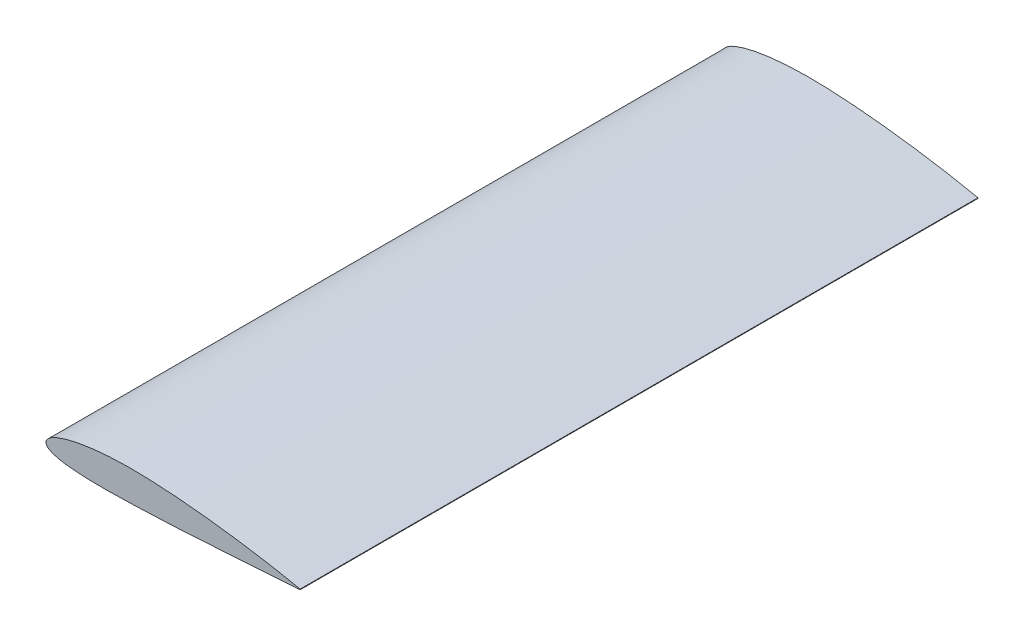
SolidWorks part; units mm, degrees
ref_plane "Plano frontal" through (0, 0, 0) normal (0, 0, 1) x (1, 0, 0)
ref_plane "Plano superior" through (0, 0, 0) normal (0, 1, 0) x (1, 0, 0)
ref_plane "Plano direito" through (0, 0, 0) normal (1, 0, 0) x (0, 0, -1)
curve "Curva1"
  spline degree 3 poles (1500.126, 1.8855, 0) (1499.3625, 2.0445, 0) (1496.3129, 2.6798, 0) (1489.4682, 4.1005, 0) (1478.1042, 6.4388, 0) (1462.2859, 9.6487, 0) (1442.1065, 13.6771, 0) (1417.6826, 18.4488, 0) (1389.1576, 23.8816, 0) (1356.6995, 29.8872, 0) (1320.4993, 36.3634, 0) (1280.7733, 43.2092, 0) (1237.7583, 50.3211, 0) (1191.7122, 57.5897, 0) (1142.9127, 64.908, 0) (1091.6565, 72.1708, 0) (1038.2553, 79.2693, 0) (983.0355, 86.0986, 0) (926.3364, 92.5608, 0) (868.5069, 98.5429, 0) (809.906, 103.958, 0) (750.8975, 108.6967, 0) (691.8509, 112.6816, 0) (633.0689, 115.8185, 0) (574.8336, 118.0666, 0) (517.5037, 119.0124, 0) (461.5248, 118.6485, 0) (407.3522, 116.9664, 0) (355.3439, 113.9866, 0) (305.8441, 109.7533, 0) (259.1775, 104.3411, 0) (215.649, 97.8407, 0) (175.5378, 90.3672, 0) (139.0976, 82.0473, 0) (106.5485, 73.0302, 0) (78.0829, 63.455, 0) (53.8515, 53.474, 0) (33.9673, 43.2199, 0) (18.4797, 32.7946, 0) (7.3977, 22.2197, 0) (0.7283, 11.2851, 0) (-0.8552, -0.0857, 0) (2.9436, -10.908, 0) (11.5766, -20.3167, 0) (24.3855, -28.5551, 0) (41.3662, -35.8908, 0) (62.4903, -42.3613, 0) (87.6694, -47.9739, 0) (116.7658, -52.7143, 0) (149.6083, -56.5782, 0) (185.9998, -59.5718, 0) (225.7233, -61.7205, 0) (268.5449, -63.0584, 0) (314.2151, -63.6414, 0) (362.4709, -63.5326, 0) (413.036, -62.8185, 0) (465.6225, -61.5859, 0) (519.931, -59.9419, 0) (575.7379, -57.9731, 0) (632.7892, -55.8169, 0) (690.7338, -53.2094, 0) (749.1366, -50.2811, 0) (807.5763, -47.0959, 0) (865.6983, -43.7442, 0) (923.1476, -40.287, 0) (979.572, -36.7918, 0) (1034.6232, -33.3034, 0) (1087.9613, -29.8708, 0) (1139.2546, -26.5308, 0) (1188.1829, -23.3117, 0) (1234.439, -20.2431, 0) (1277.7318, -17.3413, 0) (1317.7874, -14.6353, 0) (1354.3513, -12.1386, 0) (1387.1898, -9.875, 0) (1416.0927, -7.8608, 0) (1440.874, -6.1152, 0) (1461.3734, -4.6599, 0) (1477.4577, -3.5066, 0) (1489.0222, -2.6742, 0) (1495.991, -2.1677, 0) (1499.0965, -1.942, 0) (1499.874, -1.8855, 0) knots 0 0 0 0 0.000764 0.003052 0.00685 0.012132 0.018868 0.027013 0.036517 0.047321 0.059357 0.072551 0.08682 0.102077 0.118228 0.135171 0.152802 0.171013 0.18969 0.208718 0.227979 0.247354 0.266723 0.285966 0.305032 0.323824 0.342144 0.35988 0.376926 0.393182 0.408553 0.422951 0.436298 0.448523 0.459565 0.469379 0.477934 0.48522 0.491268 0.496168 0.500133 0.503587 0.507041 0.511 0.515876 0.521872 0.529071 0.537495 0.547131 0.557945 0.56989 0.582904 0.596922 0.611866 0.627656 0.644204 0.661417 0.679197 0.697443 0.716134 0.735139 0.754278 0.773432 0.792487 0.811323 0.829826 0.84788 0.865374 0.882198 0.898247 0.913421 0.927622 0.940763 0.952759 0.963533 0.973016 0.981148 0.987875 0.993154 0.996949 0.999236 1 1 1 1
sketch "Esboço2" plane through (0, 0, 0) normal (0, 0, 1) x (1, 0, 0)
  line L0 (1499.874, -1.8855) -> (1500.126, 1.8855)
  spline S0 degree 3 poles (2715.1019, 2700.4515) (1914.4321, -95.2232) (1704.9573, -40.6259) (1489.4682, 4.1005) (1478.1042, 6.4388) (1462.2859, 9.6487) (1442.1065, 13.6771) (1417.6826, 18.4488) (1389.1576, 23.8816) (1356.6995, 29.8872) (1320.4993, 36.3634) (1280.7733, 43.2092) (1237.7583, 50.3211) (1191.7122, 57.5897) (1142.9127, 64.908) (1091.6565, 72.1708) (1038.2553, 79.2693) (983.0355, 86.0986) (926.3364, 92.5608) (868.5069, 98.5429) (809.906, 103.958) (750.8975, 108.6967) (691.8509, 112.6816) (633.0689, 115.8185) (574.8336, 118.0666) (517.5037, 119.0124) (461.5248, 118.6485) (407.3522, 116.9664) (355.3439, 113.9866) (305.8441, 109.7533) (259.1775, 104.3411) (215.649, 97.8407) (175.5378, 90.3672) (139.0976, 82.0473) (106.5485, 73.0302) (78.0829, 63.455) (53.8515, 53.474) (33.9673, 43.2199) (18.4797, 32.7946) (7.3977, 22.2197) (0.7283, 11.2851) (-0.8552, -0.0857) (2.9436, -10.908) (11.5766, -20.3167) (24.3855, -28.5551) (41.3662, -35.8908) (62.4903, -42.3613) (87.6694, -47.9739) (116.7658, -52.7143) (149.6083, -56.5782) (185.9998, -59.5718) (225.7233, -61.7205) (268.5449, -63.0584) (314.2151, -63.6414) (362.4709, -63.5326) (413.036, -62.8185) (465.6225, -61.5859) (519.931, -59.9419) (575.7379, -57.9731) (632.7892, -55.8169) (690.7338, -53.2094) (749.1366, -50.2811) (807.5763, -47.0959) (865.6983, -43.7442) (923.1476, -40.287) (979.572, -36.7918) (1034.6232, -33.3034) (1087.9613, -29.8708) (1139.2546, -26.5308) (1188.1829, -23.3117) (1234.439, -20.2431) (1277.7318, -17.3413) (1317.7874, -14.6353) (1354.3513, -12.1386) (1387.1898, -9.875) (1416.0927, -7.8608) (1440.874, -6.1152) (1461.3734, -4.6599) (1477.4577, -3.5066) (1489.0222, -2.6742) (2096.1651, 41.4592) (2699.6397, 82.5696) (3151.3263, 2224.0389) knots -0.208799 -0.208799 -0.208799 -0.208799 0.000764 0.003052 0.00685 0.012132 0.018868 0.027013 0.036517 0.047321 0.059357 0.072551 0.08682 0.102077 0.118228 0.135171 0.152802 0.171013 0.18969 0.208718 0.227979 0.247354 0.266723 0.285966 0.305032 0.323824 0.342144 0.35988 0.376926 0.393182 0.408553 0.422951 0.436298 0.448523 0.459565 0.469379 0.477934 0.48522 0.491268 0.496168 0.500133 0.503587 0.507041 0.511 0.515876 0.521872 0.529071 0.537495 0.547131 0.557945 0.56989 0.582904 0.596922 0.611866 0.627656 0.644204 0.661417 0.679197 0.697443 0.716134 0.735139 0.754278 0.773432 0.792487 0.811323 0.829826 0.84788 0.865374 0.882198 0.898247 0.913421 0.927622 0.940763 0.952759 0.963533 0.973016 0.981148 0.987875 0.993154 0.996949 0.999236 1.589637 1.589637 1.589637 1.589637 only from (1500.126, 1.8855) to (1499.874, -1.8855) construction
  spline S1 degree 3 poles (1500.126, 1.8855) (1499.3625, 2.0445) (1496.3129, 2.6798) (1489.4682, 4.1005) (1478.1042, 6.4388) (1462.2859, 9.6487) (1442.1065, 13.6771) (1417.6826, 18.4488) (1389.1576, 23.8816) (1356.6995, 29.8872) (1320.4993, 36.3634) (1280.7733, 43.2092) (1237.7583, 50.3211) (1191.7122, 57.5897) (1142.9127, 64.908) (1091.6565, 72.1708) (1038.2553, 79.2693) (983.0355, 86.0986) (926.3364, 92.5608) (868.5069, 98.5429) (809.906, 103.958) (750.8975, 108.6967) (691.8509, 112.6816) (633.0689, 115.8185) (574.8336, 118.0666) (517.5037, 119.0124) (461.5248, 118.6485) (407.3522, 116.9664) (355.3439, 113.9866) (305.8441, 109.7533) (259.1775, 104.3411) (215.649, 97.8407) (175.5378, 90.3672) (139.0976, 82.0473) (106.5485, 73.0302) (78.0829, 63.455) (53.8515, 53.474) (33.9673, 43.2199) (18.4797, 32.7946) (7.3977, 22.2197) (0.7283, 11.2851) (-0.8552, -0.0857) (2.9436, -10.908) (11.5766, -20.3167) (24.3855, -28.5551) (41.3662, -35.8908) (62.4903, -42.3613) (87.6694, -47.9739) (116.7658, -52.7143) (149.6083, -56.5782) (185.9998, -59.5718) (225.7233, -61.7205) (268.5449, -63.0584) (314.2151, -63.6414) (362.4709, -63.5326) (413.036, -62.8185) (465.6225, -61.5859) (519.931, -59.9419) (575.7379, -57.9731) (632.7892, -55.8169) (690.7338, -53.2094) (749.1366, -50.2811) (807.5763, -47.0959) (865.6983, -43.7442) (923.1476, -40.287) (979.572, -36.7918) (1034.6232, -33.3034) (1087.9613, -29.8708) (1139.2546, -26.5308) (1188.1829, -23.3117) (1234.439, -20.2431) (1277.7318, -17.3413) (1317.7874, -14.6353) (1354.3513, -12.1386) (1387.1898, -9.875) (1416.0927, -7.8608) (1440.874, -6.1152) (1461.3734, -4.6599) (1477.4577, -3.5066) (1489.0222, -2.6742) (1495.991, -2.1677) (1499.0965, -1.942) (1499.874, -1.8855) knots 0 0 0 0 0.000764 0.003052 0.00685 0.012132 0.018868 0.027013 0.036517 0.047321 0.059357 0.072551 0.08682 0.102077 0.118228 0.135171 0.152802 0.171013 0.18969 0.208718 0.227979 0.247354 0.266723 0.285966 0.305032 0.323824 0.342144 0.35988 0.376926 0.393182 0.408553 0.422951 0.436298 0.448523 0.459565 0.469379 0.477934 0.48522 0.491268 0.496168 0.500133 0.503587 0.507041 0.511 0.515876 0.521872 0.529071 0.537495 0.547131 0.557945 0.56989 0.582904 0.596922 0.611866 0.627656 0.644204 0.661417 0.679197 0.697443 0.716134 0.735139 0.754278 0.773432 0.792487 0.811323 0.829826 0.84788 0.865374 0.882198 0.898247 0.913421 0.927622 0.940763 0.952759 0.963533 0.973016 0.981148 0.987875 0.993154 0.996949 0.999236 1 1 1 1
extrude "Ressalto-extrusão1" add sketch "Esboço2" along normal mid plane 4000
